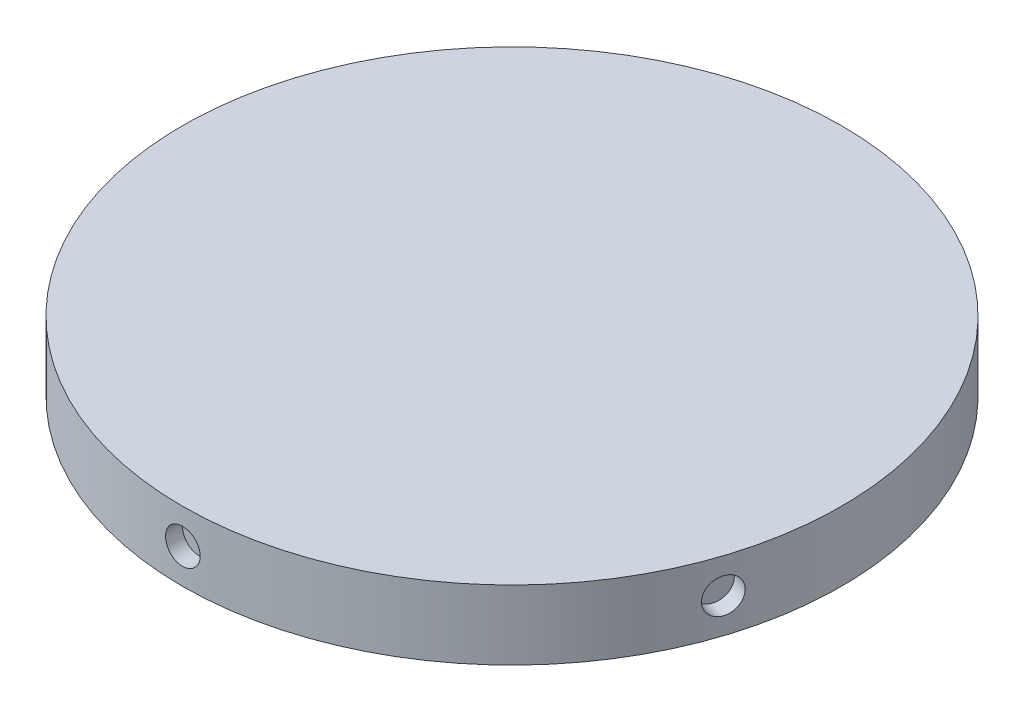
SolidWorks part; units mm, degrees
ref_plane "Front Plane" through (0, 0, 0) normal (0, 0, 1) x (1, 0, 0)
ref_plane "Top Plane" through (0, 0, 0) normal (0, 1, 0) x (1, 0, 0)
ref_plane "Right Plane" through (0, 0, 0) normal (1, 0, 0) x (0, 0, -1)
sketch "Sketch1" plane through (0, 0, 0) normal (0, 1, 0) x (1, 0, 0)
  circle A0 centre (0, 0) radius 60.325
  dimension "D1" = 120.65
extrude "Boss-Extrude1" add sketch "Sketch1" along normal blind 12.7
ref_plane "Plane1" through (0, 0, 76.2) normal (0, 0, 1) x (1, 0, 0)
sketch "Sketch2" plane through (0, 0, 76.2) normal (0, 0, 1) x (1, 0, 0)
  line L0 (0, 0) -> (0, 6.35) construction
  line L1 (-60.325, 0) -> (60.325, 0) construction
  circle A0 centre (0, 6.35) radius 3.175
  dimension "D1" = 6.35
  dimension "D2" = 6.35
extrude "Cut-Extrude1" cut sketch "Sketch2" against normal blind 19.05
pattern_curve "CrvPattern1" of "Cut-Extrude1" along edge at (0, 12.7, 60.325) parameters "D1"=5, "D3"=2.54, "D2"=1, "D4"=2.54
